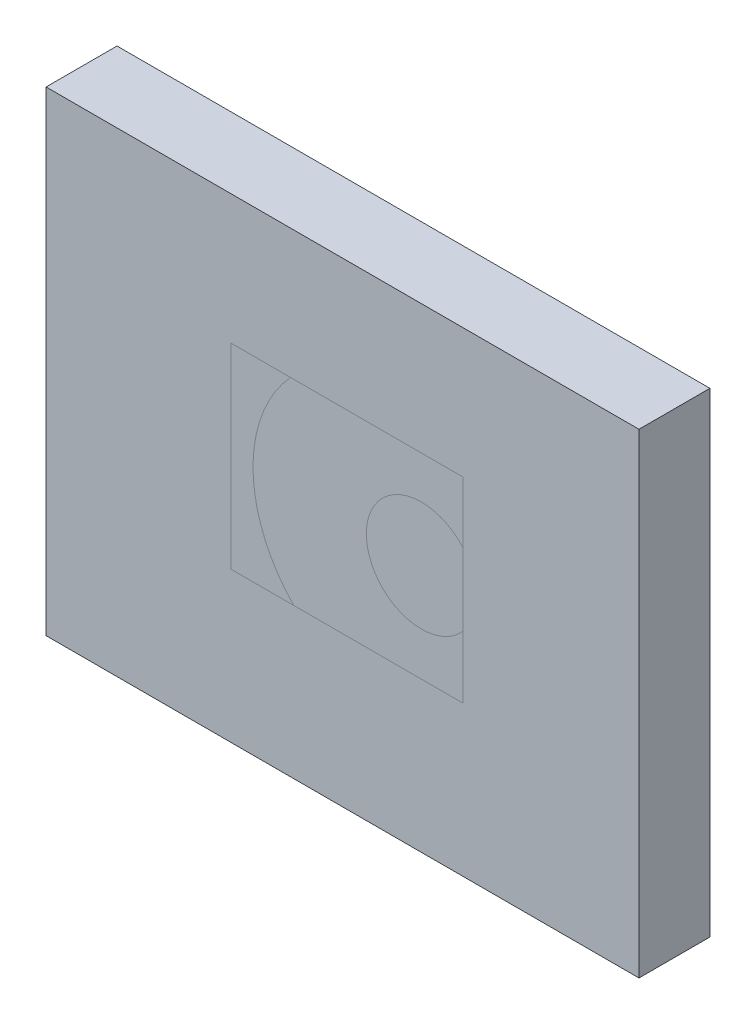
SolidWorks part; units mm, degrees
ref_plane "Ebene vorne" through (0, 0, 0) normal (0, 0, 1) x (1, 0, 0)
ref_plane "Ebene oben" through (0, 0, 0) normal (0, 1, 0) x (1, 0, 0)
ref_plane "Ebene rechts" through (0, 0, 0) normal (1, 0, 0) x (0, 0, -1)
sketch "Skizze1" plane through (0, 0, 0) normal (0, 0, 1) x (1, 0, 0)
  line L1 (0, 0) -> (82.7432, 0)
  line L2 (0, 0) -> (0, 66.32)
  line L3 (0, 66.32) -> (82.7432, 66.32)
  line L4 (82.7432, 0) -> (82.7432, 66.32)
  line L5 (25.8259, 48.2669) -> (58.171, 48.2669)
  line L6 (25.8259, 48.2669) -> (25.8259, 20.9365)
  line L7 (25.8259, 20.9365) -> (58.171, 20.9365)
  line L8 (58.171, 48.2669) -> (58.171, 20.9365)
extrude "Aufsatz-Linear austragen1" add sketch "Skizze1" against normal blind 9.9
sketch "Skizze2"
sketch_block_instance "Block1-1"
sketch_block "Block1"
surface "Oberfläche-Ebene1"
split line "Trennlinie1"
